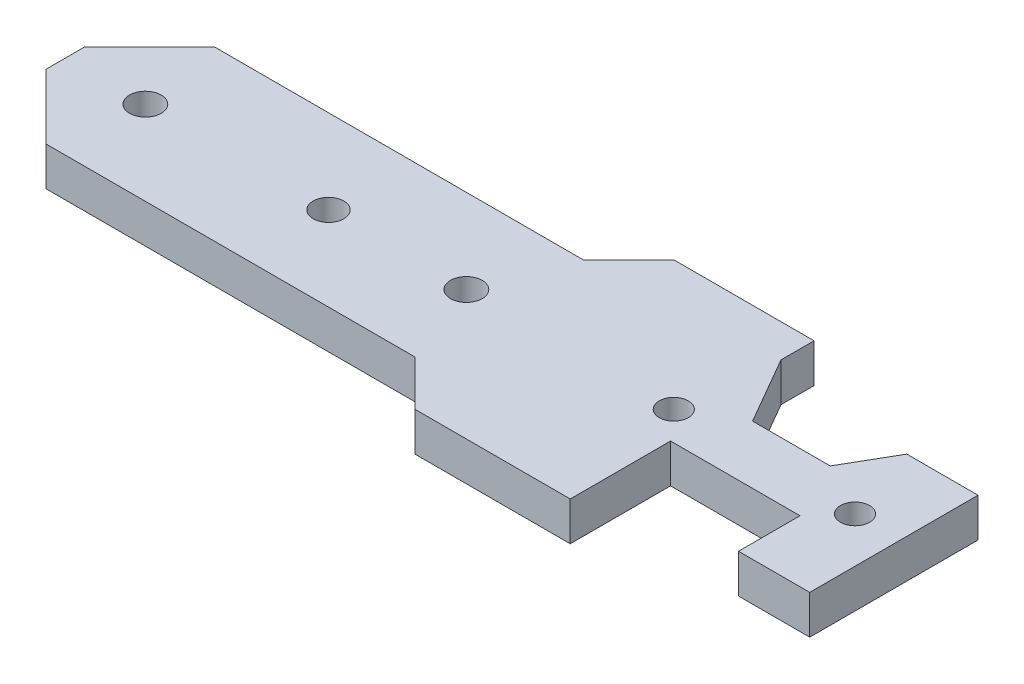
SolidWorks part; units mm, degrees
ref_plane "Front Plane" through (0, 0, 0) normal (0, 0, 1) x (1, 0, 0)
ref_plane "Top Plane" through (0, 0, 0) normal (0, 1, 0) x (1, 0, 0)
ref_plane "Right Plane" through (0, 0, 0) normal (1, 0, 0) x (0, 0, -1)
sketch "Sketch1" plane through (0, 0, 0) normal (0, 1, 0) x (1, 0, 0)
  line L0 (10, 13) -> (67, 13)
  line L1 (0, 3) -> (0, -3)
  line L2 (10, -13) -> (67, -13)
  line L3 (74, 20) -> (95.6699, 20)
  line L4 (74, -20) -> (98, -20)
  line L5 (98, -20) -> (98, -4.5)
  line L6 (98, -4.5) -> (118, -4.5)
  line L7 (118, -4.5) -> (118, -14)
  line L8 (118, -14) -> (129, -14)
  line L9 (0, 3) -> (10, 13)
  line L10 (129, -14) -> (129, 12)
  line L11 (129, 12) -> (118, 12)
  line L12 (74, 20) -> (67, 13)
  line L13 (113.6699, 4.5) -> (101.6699, 4.5)
  line L14 (0, -3) -> (10, -13)
  line L15 (95.6699, 14.8923) -> (95.6699, 20)
  line L16 (118, 12) -> (113.6699, 4.5)
  line L17 (101.6699, 4.5) -> (95.6699, 14.8923)
  line L18 (67, -13) -> (74, -20)
  point P0 (0, 13)
  point P2 (0, -13)
  point P18 (0, 0)
  dimension "D1" = 26
  dimension "D2" = 67
  dimension "D3" = 10
  dimension "D4" = 10
  dimension "D5" = 10
  dimension "D6" = 10
  dimension "D7" = 7
  dimension "D8" = 24
  dimension "D9" = 40
  dimension "D10" = 15.5
  dimension "D11" = 20
  dimension "D12" = 9.5
  dimension "D13" = 26
  dimension "D14" = 11
  dimension "D15" = 11
  dimension "D16" = 120
  dimension "D17" = 60
  dimension "D18" = 12
  dimension "D19" = 7.5
  dimension "D20" = 12
  dimension "D21" = 7
extrude "Boss-Extrude1" add sketch "Sketch1" along normal blind 6
sketch "Sketch2" plane through (0, 6, 0) normal (0, 1, 0) x (1, 0, 0)
  circle A0 centre (12.35, 0) radius 2.45
  circle A1 centre (40.65, 0) radius 2.375
  circle A2 centre (61.95, 0) radius 2.45
  circle A3 centre (94, 0) radius 2.25
  circle A4 centre (122, 0) radius 2.25
  dimension "D3" = 4.9
  dimension "D4" = 4.75
  dimension "D5" = 4.9
  dimension "D7" = 4.5
  dimension "D8" = 4.5
  dimension "D1" = 28.3
  dimension "D2" = 21.3
  dimension "D6" = 12.35
  dimension "D9" = 20
  dimension "D10" = 48
extrude "Cut-Extrude1" cut sketch "Sketch2" against normal through all
